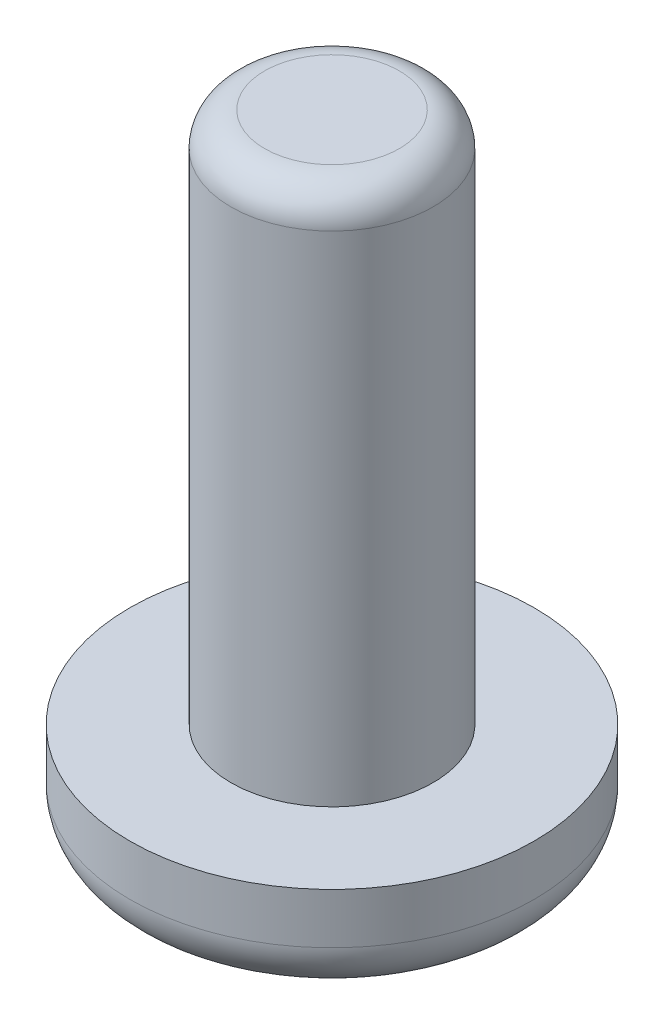
SolidWorks part; units mm, degrees
material "ABS"
ref_plane "正面" through (0, 0, 0) normal (0, 0, 1) x (1, 0, 0)
ref_plane "平面" through (0, 0, 0) normal (0, 1, 0) x (1, 0, 0)
ref_plane "右側面" through (0, 0, 0) normal (1, 0, 0) x (0, 0, -1)
sketch "ｽｹｯﾁ1" plane through (0, 0, 0) normal (0, 1, 0) x (1, 0, 0)
  circle A0 centre (0, 0) radius 6
  dimension "D1" = 12
extrude "ﾎﾞｽ - 押し出し1" add sketch "ｽｹｯﾁ1" along normal blind 3
sketch "ｽｹｯﾁ2" plane through (0, 3, 0) normal (0, 1, 0) x (1, 0, 0)
  circle A0 centre (0, 0) radius 3
  dimension "D1" = 6
extrude "ﾎﾞｽ - 押し出し2" add sketch "ｽｹｯﾁ2" along normal blind 15.8
fillet "ﾌｨﾚｯﾄ1" radius 1 1 edges at (0, 18.8, 3)
fillet "ﾌｨﾚｯﾄ2" radius 1.5 1 edges at (0, 0, 6)
